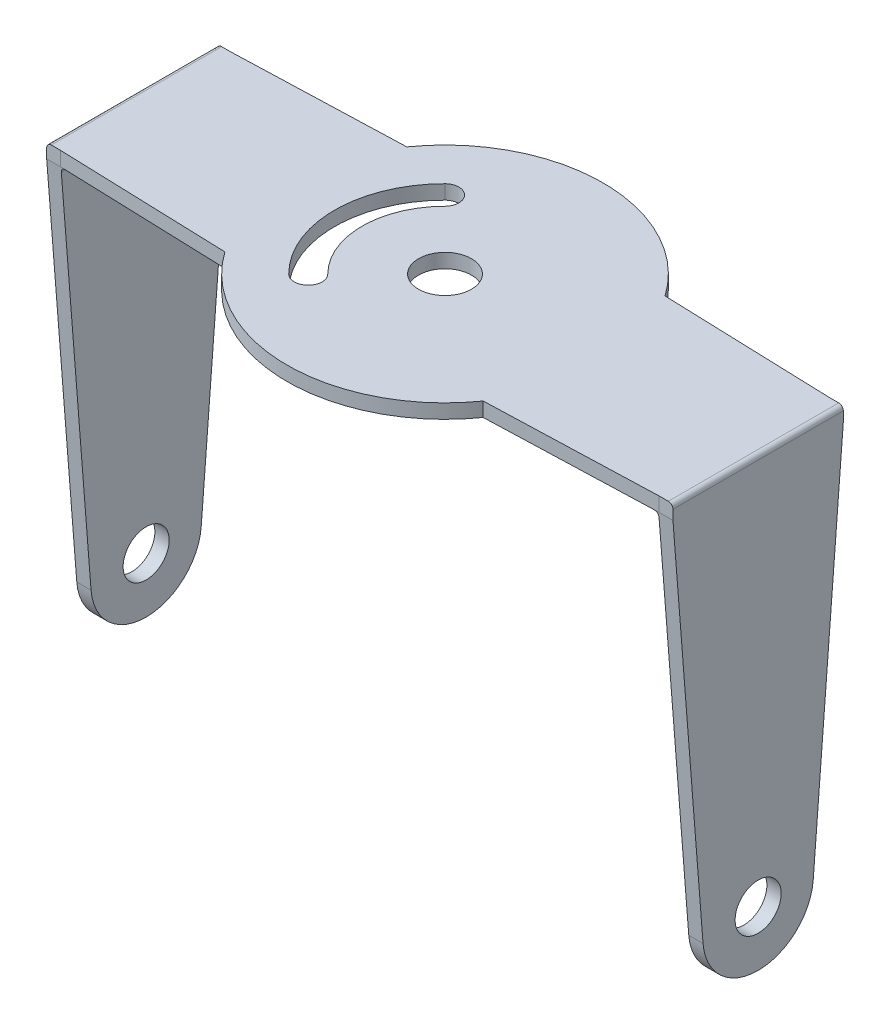
SolidWorks part; units mm, degrees
material "6061 Alloy"
ref_plane "Front Plane" through (0, 0, 0) normal (0, 0, 1) x (1, 0, 0)
ref_plane "Top Plane" through (0, 0, 0) normal (0, 1, 0) x (1, 0, 0)
ref_plane "Right Plane" through (0, 0, 0) normal (1, 0, 0) x (0, 0, -1)
sketch "Sketch1" plane through (0, 0, 0) normal (0, 0, 1) x (1, 0, 0)
  line L0 (0, 21.7352) -> (0, -18.9875) construction
  line L1 (-32.45, -6) -> (-32.45, 40.95)
  line L2 (-32.45, 40.95) -> (32.45, 40.95)
  line L3 (-32.45, -6) -> (-34, -6)
  line L4 (-34, -6) -> (-34, 42.5)
  line L5 (-34, 42.5) -> (34, 42.5)
  line L6 (34, -6) -> (34, 42.5)
  line L7 (32.45, -6) -> (34, -6)
  line L8 (32.45, -6) -> (32.45, 40.95)
  point P10 (0, 42.5)
  point P13 (0, 40.95)
  dimension "D1" = 1.55
  dimension "D2" = 1.55
  dimension "D3" = 6
  dimension "D4" = 48.5
  dimension "D5" = 68
extrude "Boss-Extrude1" add sketch "Sketch1" along normal mid plane 34.3
sketch "Sketch2" plane through (-34, 0, 0) normal (-1, 0, 0) x (0, 0, 1)
  line L0 (0, 43.6788) -> (0, -7.2434) construction
  line L1 (17.15, -6) -> (-17.15, -6) construction
  line L2 (-5.9814, -0.472) -> (-9.25, 40.95)
  line L3 (-9.25, 40.95) -> (-17.15, 40.95)
  line L4 (-17.15, 42.5) -> (-17.15, -6) construction
  line L5 (-17.15, 40.95) -> (-17.15, -6)
  line L6 (-17.15, -6) -> (0, -6)
  line L11 (17.15, 40.95) -> (-17.15, 40.95) construction
  arc A0 (-5.9814, -0.472) -> (0, -6) centre (0, 0) ccw
  point P22 (0, 0)
  point P23 (0, 0)
  point P24 (-11.4078, 40.95)
  point P26 (0, 0)
  dimension "D1" = 18.5
extrude "Cut-Extrude1" cut sketch "Sketch2" against normal through all
mirror "Mirror1" about plane through (0, 0, 0) normal (0, 0, 1) of "Cut-Extrude1"
sketch "Sketch3" plane through (0, 42.5, 0) normal (0, 1, 0) x (1, 0, 0)
  line L0 (-45.1579, 0) -> (43.1276, 0) construction
  line L1 (-32.5, -9.25) -> (-14.0217, -9.875)
  line L3 (34, -17.15) -> (-34, -17.15) construction
  line L5 (-34, -17.15) -> (0, -17.15)
  line L9 (-32.5, -9.25) -> (-34, -9.25)
  line L10 (-34, -17.15) -> (-34, 17.15) construction
  line L11 (-34, -9.25) -> (-34, -17.15)
  line L12 (-34, 9.25) -> (-34, 17.15)
  line L13 (-32.5, 9.25) -> (-34, 9.25)
  line L14 (-34, 17.15) -> (0, 17.15)
  line L15 (-32.5, 9.25) -> (-14.0217, 9.875)
  arc A0 (-14.0217, -9.875) -> (0, -17.15) centre (0, 0) ccw
  arc A2 (-14.0217, 9.875) -> (0, 17.15) centre (0, 0) cw
  dimension "D1" = 18.5
  dimension "D2" = 19.75
  dimension "D3" = 1.5
extrude "Cut-Extrude2" cut sketch "Sketch3" against normal through all
mirror "Mirror2" about plane through (0, 0, 0) normal (1, 0, 0) of "Cut-Extrude2"
sketch "Sketch4" plane through (0, 42.5, 0) normal (0, 1, 0) x (1, 0, 0)
  line L0 (-23.9185, 0) -> (15.6876, 0) construction
  circle A0 centre (0, 0) radius 2.875
  arc A2 (-7.4246, -7.4246) -> (-7.4246, 7.4246) centre (0, 0) cw construction
  arc A3 (-8.4853, 8.4853) -> (-8.4853, -8.4853) centre (0, 0) ccw
  arc A4 (-6.364, 6.364) -> (-6.364, -6.364) centre (0, 0) ccw
  arc A5 (-6.364, 6.364) -> (-8.4853, 8.4853) centre (-7.4246, 7.4246) ccw
  arc A6 (-8.4853, -8.4853) -> (-6.364, -6.364) centre (-7.4246, -7.4246) ccw
  point P5 (-10.5, 0)
  point P10 (0, 0)
  dimension "D1" = 5.75
  dimension "D2" = 1.5
  dimension "D3" = 10.5
  dimension "D4" = 90
extrude "Cut-Extrude3" cut sketch "Sketch4" against normal blind 34.3
sketch "Sketch5" plane through (-34, 0, 0) normal (-1, 0, 0) x (0, 0, 1)
  circle A0 centre (0, 0) radius 2.5
  dimension "D1" = 5
extrude "Cut-Extrude4" cut sketch "Sketch5" against normal through all
fillet "Fillet2" radius 0.5 4 edges at (34, 42.5, 0) (32.45, 40.95, 0) (-32.45, 40.95, 0) (-34, 42.5, 0)
